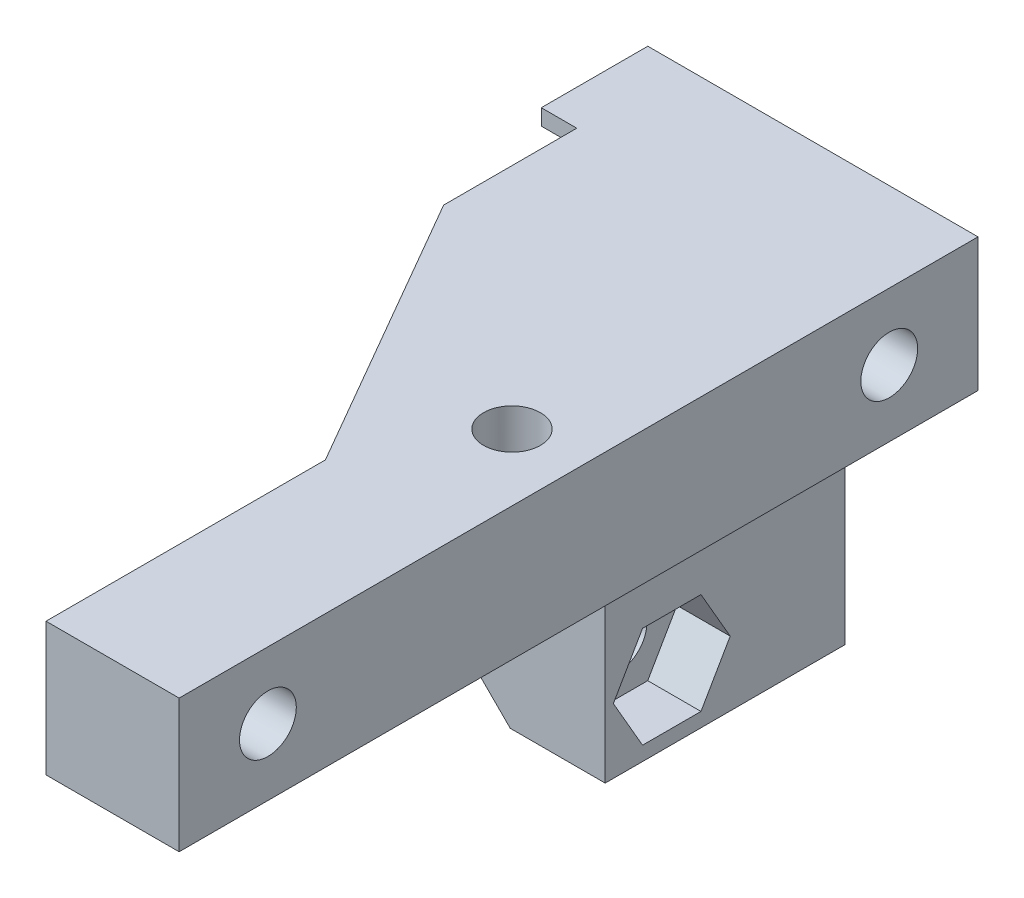
SolidWorks part; units mm, degrees
ref_plane "Alzado" through (0, 0, 0) normal (0, 0, 1) x (1, 0, 0)
ref_plane "Planta" through (0, 0, 0) normal (0, 1, 0) x (1, 0, 0)
ref_plane "Vista lateral" through (0, 0, 0) normal (1, 0, 0) x (0, 0, -1)
sketch "Croquis1" plane through (0, 0, 0) normal (0, 0, 1) x (1, 0, 0)
  line L0 (0, 0) -> (16.6, 0)
  line L1 (16.6, 0) -> (16.6, 7.5)
  line L2 (16.6, 7.5) -> (9.1, 7.5)
  line L3 (9.1, 7.5) -> (9.1, 23.65)
  line L4 (9.1, 23.65) -> (3.75, 23.65)
  line L5 (3.75, 23.65) -> (-2, 23.65)
  line L6 (0, 23.65) -> (0, 0) construction
  line L7 (0, 0) -> (-2, 0)
  line L8 (-2, 0) -> (-2, 23.65)
  line L10 (0, 0) -> (-2, 0)
  dimension "D1" = 7.5
  dimension "D3" = 3.75
  dimension "D4" = 16.6
  dimension "D5" = 7.5
  dimension "D6" = 23.65
  dimension "D7" = 2
extrude "Saliente-Extruir1" add sketch "Croquis1" along normal blind 6 contours L5 L6 L0 L1 L2 L3 L4 | L6 L5 L8 L7
sketch "Croquis2" plane through (0, 0, 6) normal (0, 0, 1) x (1, 0, 0)
  line L0 (0, 0) -> (0, 19.9)
  line L1 (0, 19.9) -> (3.75, 23.65)
  line L6 (9.1, 23.65) -> (-2, 23.65)
  line L7 (-2, 23.65) -> (-2, 0)
  line L8 (-2, 0) -> (16.6, 0)
  line L9 (16.6, 0) -> (16.6, 7.5)
  line L10 (16.6, 7.5) -> (9.1, 7.5)
  line L11 (9.1, 7.5) -> (9.1, 23.65)
  line L12 (9.1, 23.65) -> (3.75, 23.65)
  line L14 (0, 0) -> (16.6, 0)
  line L15 (16.6, 0) -> (16.6, 7.5)
  line L16 (16.6, 7.5) -> (9.1, 7.5)
  line L17 (9.1, 7.5) -> (9.1, 23.65)
  point P7 (0, 23.65)
  dimension "D4" = 3.75
  dimension "D1" = 0
extrude "Saliente-Extruir2" add sketch "Croquis2" along normal blind 7.5
sketch "Croquis3" plane through (0, 0, 0) normal (0, -1, 0) x (1, 0, 0)
  line L0 (0, 13.5) -> (9.1, 29.2617)
  line L1 (9.1, 29.2617) -> (9.1, 13.5)
  line L2 (0, 13.5) -> (16.6, 13.5) construction
  line L3 (0, 13.5) -> (9.1, 13.5)
  dimension "D1" = 7.5
  dimension "D2" = 60
extrude "Saliente-Extruir3" add sketch "Croquis3" against normal up to surface (7.5 mm away) up to face at (12.85, 7.5, 6.75)
ref_plane "Plano1" through (0, 0, 45) normal (0, 0, -1) x (-1, 0, 0)
sketch "Croquis4" plane through (0, 0, 13.5) normal (0, 0, 1) x (1, 0, 0)
  line L4 (16.6, 7.5) -> (9.1, 7.5)
  line L5 (9.1, 7.5) -> (9.1, 0)
  line L6 (9.1, 0) -> (16.6, 0)
  line L7 (16.6, 0) -> (16.6, 7.5)
  line L8 (16.6, 7.5) -> (9.1, 7.5)
  line L9 (9.1, 7.5) -> (9.1, 0)
  line L10 (9.1, 0) -> (16.6, 0)
  line L11 (16.6, 0) -> (16.6, 7.5)
  dimension "D1" = 0
extrude "Saliente-Extruir4" add sketch "Croquis4" along normal up to surface (31.5 mm away) up to plane "Plano1"
sketch "Croquis5" plane through (16.6, 0, 0) normal (1, 0, 0) x (0, 0, -1)
  line L0 (0, 3.75) -> (-5, 3.75) construction
  line L1 (0, 0) -> (0, 7.5) construction
  line L2 (-5, 3.75) -> (-40, 3.75) construction
  line L3 (-40, 3.75) -> (-45, 3.75) construction
  line L4 (-45, 7.5) -> (-45, 0) construction
  circle A0 centre (-5, 3.75) radius 1.6
  circle A1 centre (-40, 3.75) radius 1.6
  dimension "D2" = 3.2
  dimension "D1" = 35
extrude "Cortar-Extruir1" cut sketch "Croquis5" against normal up to next
sketch "Croquis6" plane through (-2, 0, 0) normal (-1, 0, 0) x (0, 0, 1)
  line L1 (3.3546, 0.9) -> (6.6454, 0.9)
  line L2 (6.6454, 0.9) -> (8.2909, 3.75)
  line L3 (8.2909, 3.75) -> (6.6454, 6.6)
  line L4 (6.6454, 6.6) -> (3.3546, 6.6)
  line L5 (3.3546, 6.6) -> (1.7091, 3.75)
  line L6 (1.7091, 3.75) -> (3.3546, 0.9)
  circle A0 centre (5, 3.75) radius 1.6 construction
  circle A1 centre (5, 3.75) radius 1.6 construction
  circle A2 centre (5, 3.75) radius 2.85 construction
  dimension "D1" = 5.7
extrude "Cortar-Extruir2" cut sketch "Croquis6" against normal offset from surface (14.1 mm away) 4.5 up to face at (16.6, 3.75, 38.4)
sketch "Croquis7" plane through (9.1, 0, 0) normal (-1, 0, 0) x (0, 0, 1)
  line L1 (38.3546, 0.9) -> (41.6454, 0.9)
  line L2 (41.6454, 0.9) -> (43.2909, 3.75)
  line L3 (43.2909, 3.75) -> (41.6454, 6.6)
  line L4 (41.6454, 6.6) -> (38.3546, 6.6)
  line L5 (38.3546, 6.6) -> (36.7091, 3.75)
  line L6 (36.7091, 3.75) -> (38.3546, 0.9)
  circle A0 centre (40, 3.75) radius 2.85 construction
  dimension "D1" = 5.7
extrude "Cortar-Extruir3" cut sketch "Croquis7" against normal blind 3
sketch "Croquis8" plane through (0, 0, 0) normal (0, -1, 0) x (1, 0, 0)
  line L0 (12.85, 45) -> (12.85, 0) construction
  line L1 (16.6, 45) -> (9.1, 45) construction
  line L2 (-2, 0) -> (16.6, 0) construction
  circle A0 centre (12.85, 22.5) radius 1.6
  dimension "D1" = 3.2
extrude "Cortar-Extruir4" cut sketch "Croquis8" against normal up to next
sketch "Croquis9" plane through (0, 7.5, 0) normal (0, 1, 0) x (1, 0, 0)
  line L1 (15.7, -20.8546) -> (12.85, -19.2091)
  line L2 (12.85, -19.2091) -> (10, -20.8546)
  line L3 (10, -20.8546) -> (10, -24.1454)
  line L4 (10, -24.1454) -> (12.85, -25.7909)
  line L5 (12.85, -25.7909) -> (15.7, -24.1454)
  line L6 (15.7, -24.1454) -> (15.7, -20.8546)
  circle A0 centre (12.85, -22.5) radius 2.85 construction
  dimension "D1" = 5.7
extrude "Cortar-Extruir5" cut sketch "Croquis9" against normal blind 3
sketch "Croquis10" plane through (9.1, 0, 0) normal (1, 0, 0) x (0, 0, -1)
  line L0 (-13.5, 23.65) -> (-6, 23.65) construction
  line L1 (-13.5, 23.65) -> (-6, 23.65) construction
  line L2 (-9.75, 23.65) -> (-9.75, 20) construction
  circle A0 centre (-9.75, 20) radius 1.6
  dimension "D1" = 3.2
  dimension "D2" = 3.65
extrude "Cortar-Extruir6" cut sketch "Croquis10" against normal up to next
sketch "Croquis11" plane through (9.1, 0, 0) normal (1, 0, 0) x (0, 0, -1)
  line L1 (-8.1046, 22.85) -> (-11.3954, 22.85)
  line L2 (-11.3954, 22.85) -> (-13.0409, 20)
  line L3 (-13.0409, 20) -> (-11.3954, 17.15)
  line L4 (-11.3954, 17.15) -> (-8.1046, 17.15)
  line L5 (-8.1046, 17.15) -> (-6.4591, 20)
  line L6 (-6.4591, 20) -> (-8.1046, 22.85)
  circle A0 centre (-9.75, 20) radius 2.85 construction
  dimension "D1" = 5.7
extrude "Cortar-Extruir7" cut sketch "Croquis11" against normal blind 3
mirror "Simetría1" about plane through (0, 0, 0) normal (0, 1, 0) of bodies 111
delete or keep bodies "Sólido-Eliminar1" type delete bodies bodies 111
